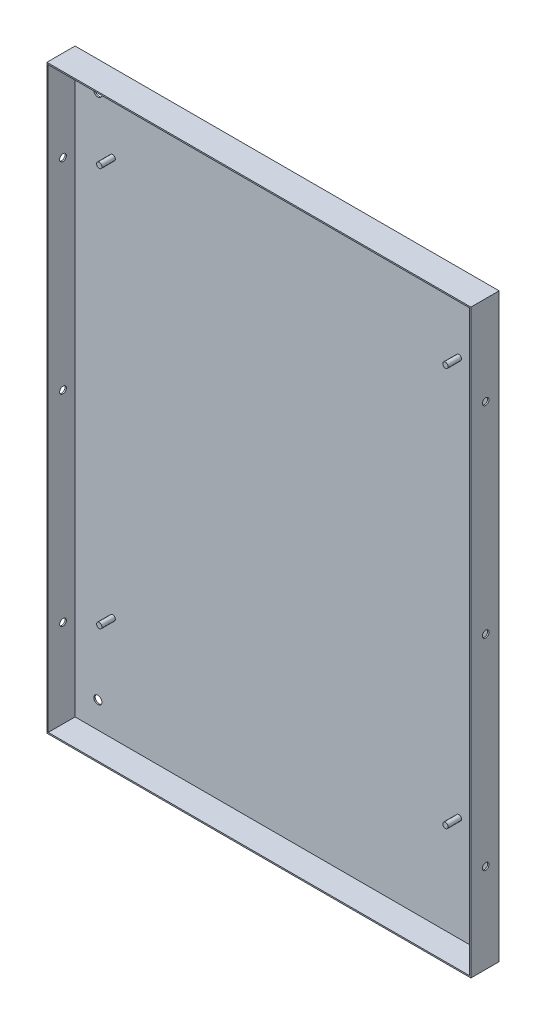
SolidWorks part; units mm, degrees
ref_plane "Alzado" through (0, 0, 0) normal (0, 0, 1) x (1, 0, 0)
ref_plane "Planta" through (0, 0, 0) normal (0, 1, 0) x (1, 0, 0)
ref_plane "Vista lateral" through (0, 0, 0) normal (1, 0, 0) x (0, 0, -1)
sketch "Croquis1" plane through (0, 0, 0) normal (0, 0, 1) x (1, 0, 0)
  line L0 (-316, 216.5) -> (-459.9713, 216.5) construction
  line L1 (0, 0) -> (-316, 0)
  line L2 (0, 0) -> (0, 433)
  line L3 (0, 433) -> (-316, 433)
  line L4 (-316, 0) -> (-316, 433)
  dimension "D1" = 316
  dimension "D2" = 433
extrude "Saliente-Extruir3" add sketch "Croquis1" along normal blind 1
sketch "Croquis2" plane through (0, 0, 1) normal (0, 0, 1) x (1, 0, 0)
  line L0 (0, 0) -> (0, 433) construction
  line L1 (-316, 433) -> (0, 433)
  line L2 (-316, 433) -> (-316, 432)
  line L3 (-315, 432) -> (-1, 432)
  line L4 (0, 433) -> (0, 432)
  line L5 (-316, 0) -> (0, 0) construction
  line L6 (-316, 433) -> (-315, 433)
  line L7 (-316, 433) -> (-316, 0)
  line L8 (-316, 0) -> (-315, 0)
  line L9 (-315, 432) -> (-315, 1)
  line L11 (-316, 0) -> (0, 0)
  line L12 (-316, 0) -> (-316, 1)
  line L13 (-315, 1) -> (-1, 1)
  line L14 (0, 0) -> (0, 1)
  line L15 (0, 0) -> (-1, 0)
  line L16 (0, 0) -> (0, 432)
  line L18 (-1, 1) -> (-1, 432)
  line M17 (0, 0) -> (0, 433)
  line M18 (0, 433) -> (-316, 433)
  line M19 (-316, 433) -> (-316, 0)
  line M20 (-316, 0) -> (0, 0)
  dimension "D1" = 1
  dimension "D2" = 1
  dimension "D3" = 1
  dimension "D4" = 1
extrude "Saliente-Extruir4" add sketch "Croquis2" along normal blind 20 contours L11 L1 L7 L18 L13 L9 L3 M20 M17 M18 M19
sketch "Croquis3" plane through (0, 0, 1) normal (0, 0, 1) x (1, 0, 0)
  line L0 (-315, 216.5) -> (-390.1233, 216.5) construction
  line L1 (-315, 432) -> (-315, 1) construction
  line L2 (-316, 433) -> (-316, 0) construction
  line L3 (-158, 432) -> (-158, 470.5538) construction
  line L4 (-315, 432) -> (-1, 432) construction
  line L6 (-287, 376) -> (-287, -21.6387) construction
  line L7 (-29, 376) -> (-29, 57.4362) construction
  circle A0 centre (-287, 376) radius 2
  circle A3 centre (-29, 376) radius 2
  circle A4 centre (-287, 79) radius 2
  circle A5 centre (-29, 79) radius 2
  dimension "D1" = 4
  dimension "D4" = 4
  dimension "D2" = 29
  dimension "D3" = 159.5
  dimension "D5" = 137.5
extrude "Saliente-Extruir5" add sketch "Croquis3" along normal blind 10
sketch "Croquis4" plane through (0, 0, 0) normal (1, 0, 0) x (0, 0, -1)
  line L0 (0, 216.5) -> (-158.0043, 216.5) construction
  line L1 (0, 0) -> (0, 433) construction
  circle A0 centre (-10, 366.5) radius 2.5
  circle A1 centre (-10, 66.5) radius 2.5
  circle A2 centre (-10, 216.5) radius 2.5
  dimension "D1" = 5
  dimension "D4" = 5
  dimension "D2" = 150
  dimension "D3" = 10
  dimension "D5" = 10
extrude "Cortar-Extruir1" cut sketch "Croquis4" against normal up to surface (316 mm away) up to face at (-316, 216.5, 10.5)
sketch "Croquis5" plane through (0, 0, 1) normal (0, 0, 1) x (1, 0, 0)
  line L0 (0, 433) -> (-316, 433) construction
  line L1 (-316, 433) -> (-316, 0) construction
  line L2 (-158, 433) -> (-158, 481.9609) construction
  line L3 (-315, 216.5) -> (-146.3491, 216.5) construction
  line L4 (-315, 432) -> (-315, 1) construction
  circle A0 centre (-298, 412.5) radius 3
  circle A1 centre (-298, 20.5) radius 3
  circle A2 centre (-18, 412.5) radius 3
  circle A3 centre (-18, 20.5) radius 3
  dimension "D1" = 6
  dimension "D2" = 20.5
  dimension "D3" = 18
extrude "Cortar-Extruir2" cut sketch "Croquis5" against normal up to surface (1 mm away) up to face at (-158, 216.5, 0)
